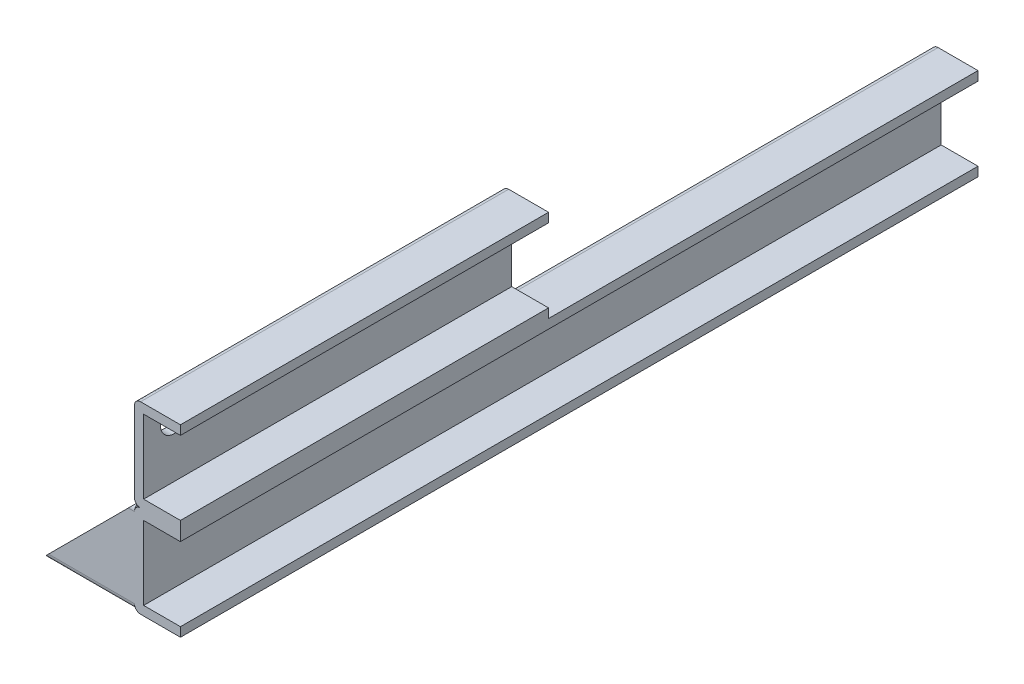
SolidWorks part; units mm, degrees
ref_plane "Alzado" through (0, 0, 0) normal (0, 0, 1) x (1, 0, 0)
ref_plane "Planta" through (0, 0, 0) normal (0, 1, 0) x (1, 0, 0)
ref_plane "Vista lateral" through (0, 0, 0) normal (1, 0, 0) x (0, 0, -1)
sketch "Croquis1" plane through (0, 0, 0) normal (0, 0, 1) x (1, 0, 0)
  line L0 (-12, 12) -> (0, 12)
  line L1 (-15, 15) -> (0, 15)
  line L2 (-15, 15) -> (-15, -15)
  line L3 (-15, -15) -> (0, -15)
  line L4 (-12, 12) -> (-12, -12)
  line L5 (-12, -12) -> (0, -12)
  line L6 (0, 12) -> (0, 15)
  line L7 (0, -15) -> (0, -12)
  dimension "D1" = 30
  dimension "D2" = 15
  dimension "D3" = 15
  dimension "D4" = 3
extrude "Saliente-Extruir1" add sketch "Croquis1" along normal mid plane 260
fillet "Redondeo1" radius 2 2 edges at (-15, -15, 0) (-15, 15, 0)
sketch "Croquis2" plane through (0, 0, 130) normal (0, 0, 1) x (1, 0, 0)
  line L0 (0, 12) -> (0, 15) construction
  line L1 (0, 15) -> (-13, 15) construction
  line L16 (-15, 43) -> (-15, 17)
  line L17 (-13, 15) -> (0, 15)
  line L18 (0, 15) -> (0, 18)
  line L19 (0, 18) -> (-12, 18)
  line L20 (-12, 18) -> (-12, 42)
  line L21 (-12, 42) -> (0, 42)
  line L22 (0, 42) -> (0, 45)
  line L23 (0, 45) -> (-13, 45)
  arc A0 (-15, 17) -> (-13, 15) centre (-13, 17) ccw
  arc A1 (-15, 43) -> (-13, 45) centre (-13, 43) cw
  point P12 (0, 0)
  point P15 (-15, 15)
  point P18 (-15, 45)
  dimension "D5" = 2
  dimension "D1" = 30
  dimension "D2" = 3
  dimension "D3" = 15
  dimension "D4" = 12
extrude "Saliente-Extruir2" add sketch "Croquis2" against normal blind 120
sketch "Croquis3" plane through (-15, 0, 0) normal (-1, 0, 0) x (0, 0, 1)
  line L0 (130, 43) -> (130, 17) construction
  line L1 (10, 45) -> (130, 45) construction
  circle A0 centre (120, 36) radius 4.5
  circle A1 centre (20, 36) radius 4.5
  point P4 (0, 0)
  point P7 (130, 30)
  dimension "D1" = 9
  dimension "D2" = 10
  dimension "D3" = 110
  dimension "D4" = 9
extrude "Cortar-Extruir1" cut sketch "Croquis3" against normal blind 20
sketch "Croquis4" plane through (-15, 0, 0) normal (-1, 0, 0) x (0, 0, 1)
  line L1 (128, -15) -> (102, -15)
  line L2 (130, -13) -> (130, 13)
  line L3 (128, 15) -> (102, 15)
  line L4 (100, -13) -> (100, 13)
  line L5 (127, -12) -> (103, -12)
  line L6 (103, -12) -> (103, 12)
  line L7 (127, 12) -> (103, 12)
  line L8 (127, -12) -> (127, 12)
  line L9 (130, -15) -> (130, 15) construction
  line L10 (130, 15) -> (100, 15) construction
  line L11 (130, -15) -> (100, -15) construction
  line L12 (100, -15) -> (100, 15) construction
  arc A0 (130, 13) -> (128, 15) centre (128, 13) ccw
  arc A1 (128, -15) -> (130, -13) centre (128, -13) ccw
  arc A2 (102, -15) -> (100, -13) centre (102, -13) cw
  arc A3 (102, 15) -> (100, 13) centre (102, 13) ccw
  dimension "D3" = 2
  dimension "D2" = 3
extrude "Saliente-Extruir3" add sketch "Croquis4" along normal blind 30
sketch "Croquis5" plane through (0, 0, 130) normal (0, 0, 1) x (1, 0, 0)
  line L0 (-45, -15) -> (-15, 15)
  line L1 (-15, 15) -> (-45, 15)
  line L2 (-45, 15) -> (-45, -15)
extrude "Cortar-Extruir2" cut sketch "Croquis5" against normal blind 50
sketch "Croquis6" plane through (0, -12, 0) normal (0, 1, 0) x (1, 0, 0)
  circle A0 centre (-30.5282, -114.6163) radius 3.5
  point P2 (-30.5282, -114.6163)
  dimension "D1" = 7
